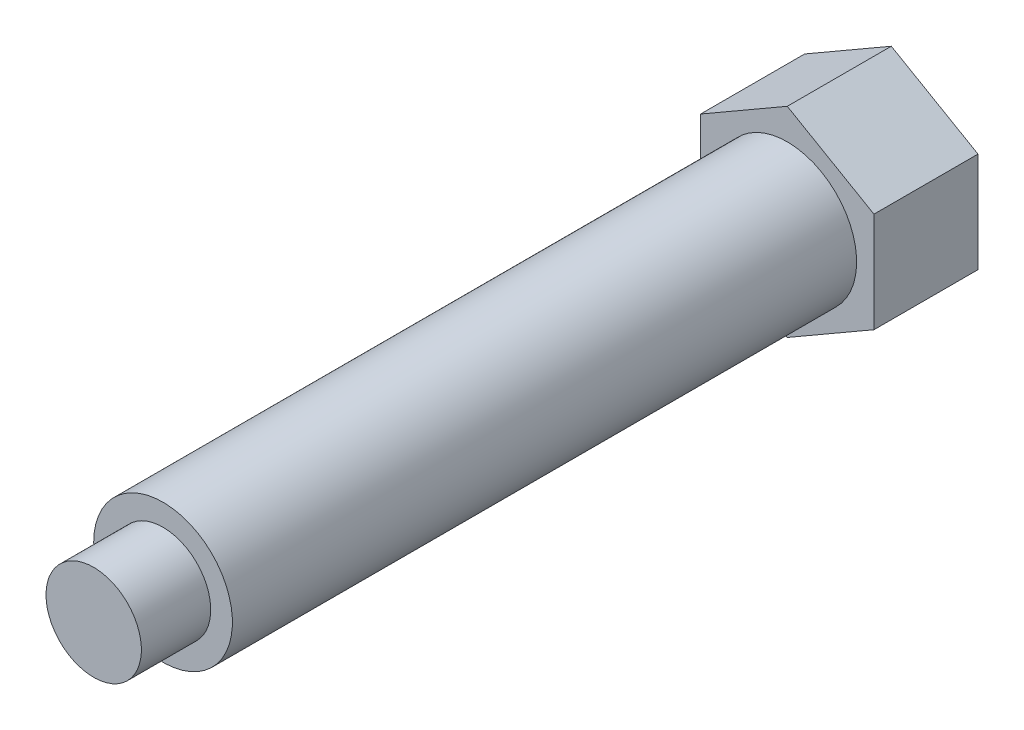
SolidWorks part; units mm, degrees
ref_plane "Спереди" through (0, 0, 0) normal (0, 0, 1) x (1, 0, 0)
ref_plane "Сверху" through (0, 0, 0) normal (0, 1, 0) x (1, 0, 0)
ref_plane "Справа" through (0, 0, 0) normal (1, 0, 0) x (0, 0, -1)
sketch "Sketch1" plane through (0, 0, 0) normal (0, 1, 0) x (1, 0, 0)
  line L0 (0, 0) -> (0, -40)
  line L1 (0, -40) -> (2.75, -40)
  line L2 (2.75, -40) -> (2.75, -36)
  line L3 (2.75, -36) -> (4, -36)
  line L4 (4, -36) -> (4, 0)
  line L5 (0, 0) -> (4, 0)
  line L6 (0, 1.1873) -> (0, -43.9301) construction
  dimension "D" = 8
  dimension "L" = 40
  dimension "DP" = 5.5
  dimension "Z2" = 4
revolve "Base-Revolve" add sketch "Sketch1"
cosmetic thread "Cosmetic Thread1"
extrude "Boss-Extrude1" add sketch "Sketch2" along normal blind 6
sketch "Sketch2" plane through (0, 0, 0) normal (0, 0, -1) x (-1, 0, 0)
  line L1 (5, -2.8868) -> (5, 2.8868)
  line L2 (5, 2.8868) -> (0, 5.7735)
  line L3 (0, 5.7735) -> (-5, 2.8868)
  line L4 (-5, 2.8868) -> (-5, -2.8868)
  line L5 (-5, -2.8868) -> (0, -5.7735)
  line L6 (0, -5.7735) -> (5, -2.8868)
  circle A0 centre (0, 0) radius 5 construction
  dimension "S" = 10
